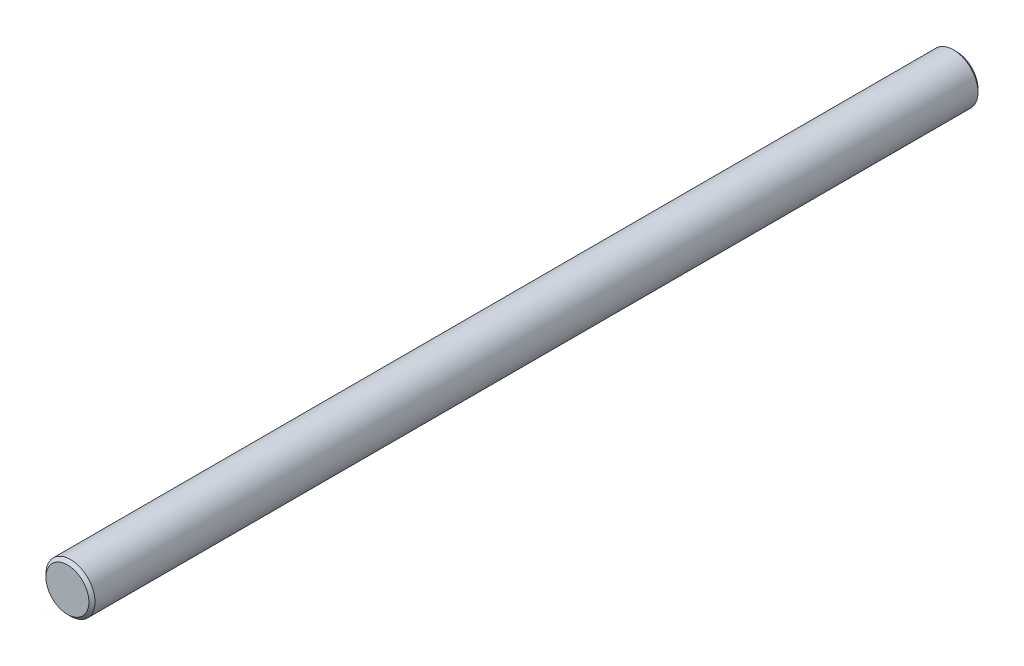
SolidWorks part; units mm, degrees
material "AISI 1020 Steel, Cold Rolled"
ref_plane "Front Plane" through (0, 0, 0) normal (0, 0, 1) x (1, 0, 0)
ref_plane "Top Plane" through (0, 0, 0) normal (0, 1, 0) x (1, 0, 0)
ref_plane "Right Plane" through (0, 0, 0) normal (1, 0, 0) x (0, 0, -1)
sketch "Sketch2" plane through (0, 0, 0) normal (0, 0, 1) x (1, 0, 0)
  circle A0 centre (0, 0) radius 4
  dimension "D1" = 8
extrude "Boss-Extrude1" add sketch "Sketch2" along normal blind 145
chamfer "Chamfer1" distance 0.5 angle 45 2 edges at (4, 0, 145) (4, 0, 0)
